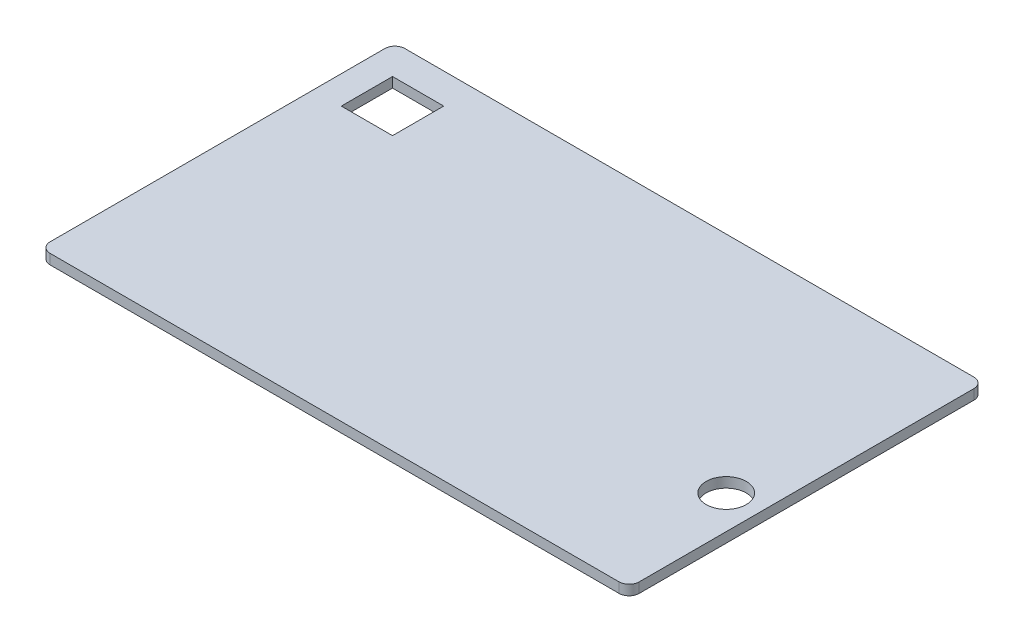
SolidWorks part; units mm, degrees
ref_plane "Plan de face" through (0, 0, 0) normal (0, 0, 1) x (1, 0, 0)
ref_plane "Plan de dessus" through (0, 0, 0) normal (0, 1, 0) x (1, 0, 0)
ref_plane "Plan de droite" through (0, 0, 0) normal (1, 0, 0) x (0, 0, -1)
sketch "Esquisse1" plane through (0, 0, 0) normal (0, 1, 0) x (1, 0, 0)
  line L1 (-88, -53) -> (88, -53)
  line L2 (-88, -53) -> (-88, 53)
  line L3 (-88, 53) -> (88, 53)
  line L4 (88, -53) -> (88, 53)
  line L5 (-88, -53) -> (88, 53) construction
  line L6 (-88, 53) -> (88, -53) construction
  point P0 (0, 0)
  dimension "D1" = 176
  dimension "D2" = 106
extrude "Boss.-Extru.1" add sketch "Esquisse1" along normal blind 3
fillet "Congé1" radius 3 4 edges at (88, 1.5, -53) (88, 1.5, 53) (-88, 1.5, -53) (-88, 1.5, 53)
sketch "Esquisse3" plane through (0, 0, 0) normal (0, -1, 0) x (1, 0, 0)
  line L0 (78, -53) -> (78, 14) construction
  line L1 (85, -53) -> (-85, -53) construction
  line L2 (88, 50) -> (88, -50) construction
  circle A0 centre (78, 14) radius 6
  dimension "D1" = 10
extrude "Enlèv. mat.-Extru.2" cut sketch "Esquisse3" against normal blind 10
sketch "Esquisse4" plane through (0, 0, 0) normal (0, -1, 0) x (1, 0, 0)
  line L1 (-79.6116, -43.9134) -> (-64.3116, -43.9134)
  line L2 (-79.6116, -43.9134) -> (-79.6116, -28.6134)
  line L3 (-79.6116, -28.6134) -> (-64.3116, -28.6134)
  line L4 (-64.3116, -43.9134) -> (-64.3116, -28.6134)
  dimension "D1" = 15.3
  dimension "D2" = 15.3
extrude "Enlèv. mat.-Extru.3" cut sketch "Esquisse4" against normal blind 10
